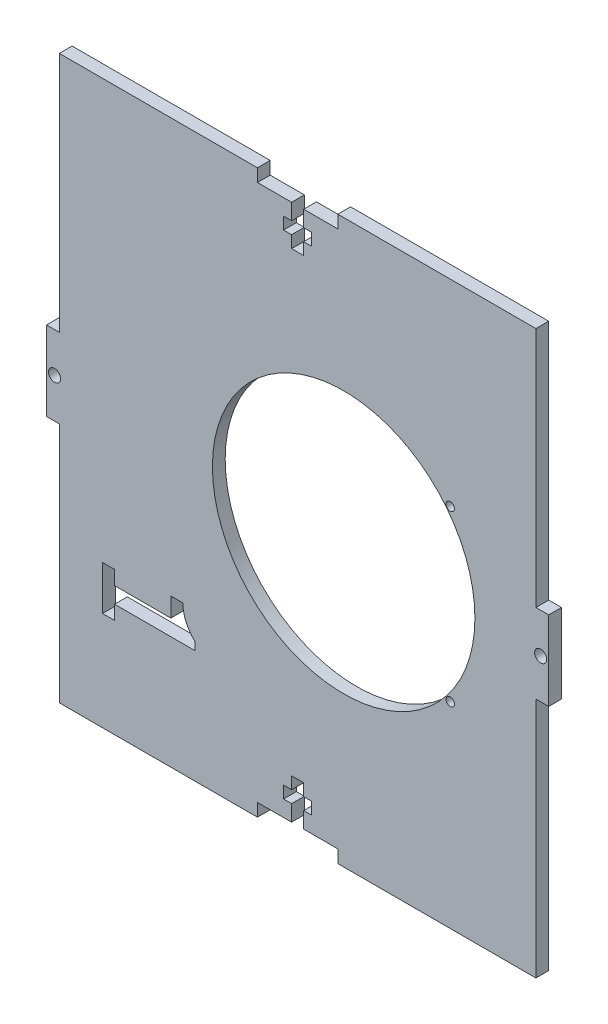
SolidWorks part; units mm, degrees
ref_plane "Front Plane" through (0, 0, 0) normal (0, 0, 1) x (1, 0, 0)
ref_plane "Top Plane" through (0, 0, 0) normal (0, 1, 0) x (1, 0, 0)
ref_plane "Right Plane" through (0, 0, 0) normal (1, 0, 0) x (0, 0, -1)
sketch "Sketch1" plane through (0, 0, 0) normal (0, 0, 1) x (1, 0, 0)
  line L1 (-62.5, 70) -> (62.5, 70)
  line L2 (-62.5, 70) -> (-62.5, -70)
  line L3 (-62.5, -70) -> (62.5, -70)
  line L4 (62.5, 70) -> (62.5, -70)
  line L5 (-62.5, 70) -> (62.5, -70) construction
  line L6 (-62.5, -70) -> (62.5, 70) construction
  point P0 (0, 0)
  dimension "D1" = 140
  dimension "D2" = 125
extrude "Boss-Extrude1" add sketch "Sketch1" along normal blind 3.18
sketch "Sketch2" plane through (0, 0, 3.18) normal (0, 0, 1) x (1, 0, 0)
  line L0 (0, 0) -> (62.5, 0) construction
  line L1 (-10, 70) -> (10, 70)
  line L2 (-10, 70) -> (-10, 66.82)
  line L3 (-10, 66.82) -> (-1.5, 66.82)
  line L4 (10, 70) -> (10, 66.82)
  line L5 (62.5, -70) -> (62.5, 70) construction
  line L6 (0, 0) -> (0, 70) construction
  line L7 (-1.5, 56.82) -> (1.5, 56.82)
  line L8 (-1.5, 56.82) -> (-1.5, 59.82)
  line L10 (1.5, 56.82) -> (1.5, 59.82)
  line L12 (62.5, 70) -> (-62.5, 70) construction
  line L13 (3.5, 62.82) -> (1.5, 62.82)
  line L14 (3.5, 62.82) -> (3.5, 59.82)
  line L15 (3.5, 59.82) -> (1.5, 59.82)
  line L16 (-3.5, 62.82) -> (-3.5, 59.82)
  line L17 (-10, -70) -> (-10, -66.82)
  line L18 (-10, -66.82) -> (-1.5, -66.82)
  line L19 (-1.5, -62.82) -> (-1.5, -66.82)
  line L20 (-1.5, -62.82) -> (-3.5, -62.82)
  line L21 (-3.5, -62.82) -> (-3.5, -59.82)
  line L22 (1.5, 66.82) -> (10, 66.82)
  line L23 (-1.5, 62.82) -> (-3.5, 62.82)
  line L24 (-1.5, -59.82) -> (-3.5, -59.82)
  line L25 (-1.5, -56.82) -> (-1.5, -59.82)
  line L26 (-1.5, -56.82) -> (1.5, -56.82)
  line L27 (-1.5, 59.82) -> (-3.5, 59.82)
  line L28 (1.5, -56.82) -> (1.5, -59.82)
  line L29 (-1.5, 62.82) -> (-1.5, 66.82)
  line L30 (1.5, 62.82) -> (1.5, 66.82)
  line L31 (3.5, -59.82) -> (1.5, -59.82)
  line L32 (3.5, -62.82) -> (3.5, -59.82)
  line L33 (3.5, -62.82) -> (1.5, -62.82)
  line L34 (1.5, -62.82) -> (1.5, -66.82)
  line L35 (1.5, -66.82) -> (10, -66.82)
  line L36 (10, -70) -> (10, -66.82)
  line L37 (-10, -70) -> (10, -70)
  line L38 (-62.5, 70) -> (-62.5, -70) construction
  line L39 (-62.5, 70) -> (-59.32, 70)
  line L40 (-62.5, 70) -> (-62.5, 9.875)
  line L41 (-62.5, 9.875) -> (-59.32, 9.875)
  line L42 (-59.32, 70) -> (-59.32, 9.875)
  line L43 (-62.5, -70) -> (-59.32, -70)
  line L44 (-62.5, -70) -> (-62.5, -9.875)
  line L45 (-62.5, -9.875) -> (-59.32, -9.875)
  line L46 (-59.32, -70) -> (-59.32, -9.875)
  line L47 (62.5, -9.875) -> (59.32, -9.875)
  line L48 (59.32, -70) -> (59.32, -9.875)
  line L49 (62.5, -70) -> (59.32, -70)
  line L50 (62.5, -70) -> (62.5, -9.875)
  line L51 (62.5, 9.875) -> (59.32, 9.875)
  line L52 (59.32, 70) -> (59.32, 9.875)
  line L53 (62.5, 70) -> (59.32, 70)
  line L54 (62.5, 70) -> (62.5, 9.875)
  circle A0 centre (-60.5, 0) radius 1.5
  circle A1 centre (60.5, 0) radius 1.5
  point P0 (0, 50.5662)
  point P5 (0, 32.0079)
  point P10 (15.4931, 34.4893)
  dimension "D11" = 3
  dimension "D12" = 2
  dimension "D1" = 20
  dimension "D2" = 19.75
  dimension "D3" = 4
  dimension "D4" = 3
  dimension "D5" = 3.18
  dimension "D6" = 7
  dimension "D7" = 3
  dimension "D8" = 3
  dimension "D9" = 3.18
  dimension "D10" = 3.18
extrude "Cut-Extrude1" cut sketch "Sketch2" against normal through all
sketch "Sketch4" plane through (0, 0, 0) normal (0, 0, 1) x (1, 0, 0)
  line L3 (-25.5711, -41.8625) -> (-45.5711, -41.8625)
  line L4 (-45.5711, -41.8625) -> (-45.5711, -45.3625)
  line L5 (-45.5711, -45.3625) -> (-48.5711, -45.3625)
  line L6 (-48.5711, -45.3625) -> (-48.5711, -34.3625)
  line L7 (-48.5711, -34.3625) -> (-45.5711, -34.3625)
  line L8 (-45.5711, -34.3625) -> (-45.5711, -37.8625)
  line L9 (-45.5711, -37.8625) -> (-31.5711, -37.8625)
  line L10 (-31.5711, -37.8625) -> (-31.5711, -33.0876)
  line L11 (-31.5711, -33.0876) -> (-28.5711, -33.0876)
  line L12 (-25.5711, -39.8625) -> (-25.5711, -41.8625)
  arc A0 (-28.5711, -33.0876) -> (-25.5711, -39.8625) centre (-19.4212, -33.0876) ccw
  dimension "D1" = 11
  dimension "D2" = 4
  dimension "D3" = 3
  dimension "D4" = 3
  dimension "D5" = 14
  dimension "D6" = 20
  dimension "D7" = 3
extrude "Cut-Extrude5" cut sketch "Sketch4" along normal blind 12
sketch "Sketch5" plane through (0, 0, 3.18) normal (0, 0, 1) x (1, 0, 0)
  circle A0 centre (11.4626, 0) radius 32.6714
extrude "Cut-Extrude6" cut sketch "Sketch5" against normal blind 10
sketch "Sketch9" plane through (0, 0, 3.18) normal (0, 0, 1) x (1, 0, 0)
  circle A0 centre (37.9914, -21.1) radius 1.042
  circle A1 centre (37.9914, 21.0083) radius 1.042
extrude "Cut-Extrude8" cut sketch "Sketch9" against normal through all
